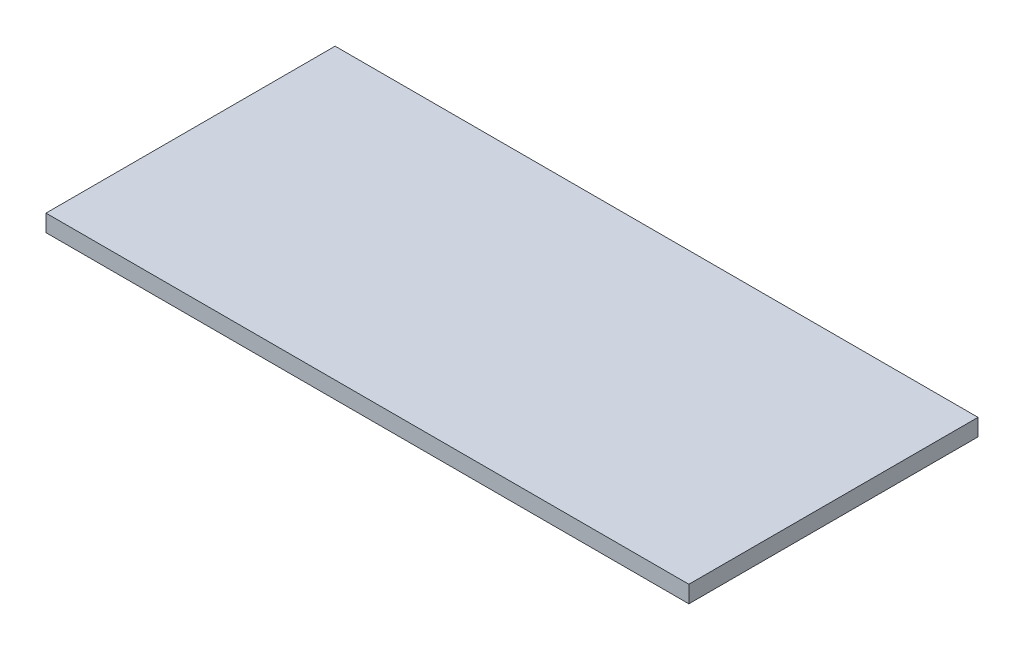
SolidWorks part; units mm, degrees
ref_plane "Front Plane" through (0, 0, 0) normal (0, 0, 1) x (1, 0, 0)
ref_plane "Top Plane" through (0, 0, 0) normal (0, 1, 0) x (1, 0, 0)
ref_plane "Right Plane" through (0, 0, 0) normal (1, 0, 0) x (0, 0, -1)
sketch "Sketch1" plane through (0, 0, 0) normal (0, 1, 0) x (1, 0, 0)
  line L1 (0, 0) -> (60.1472, 0)
  line L2 (0, 0) -> (0, 27.051)
  line L3 (0, 27.051) -> (60.1472, 27.051)
  line L4 (60.1472, 0) -> (60.1472, 27.051)
  dimension "D1" = 60.1472
  dimension "D2" = 27.051
extrude "Boss-Extrude1" add sketch "Sketch1" along normal blind 1.5875
